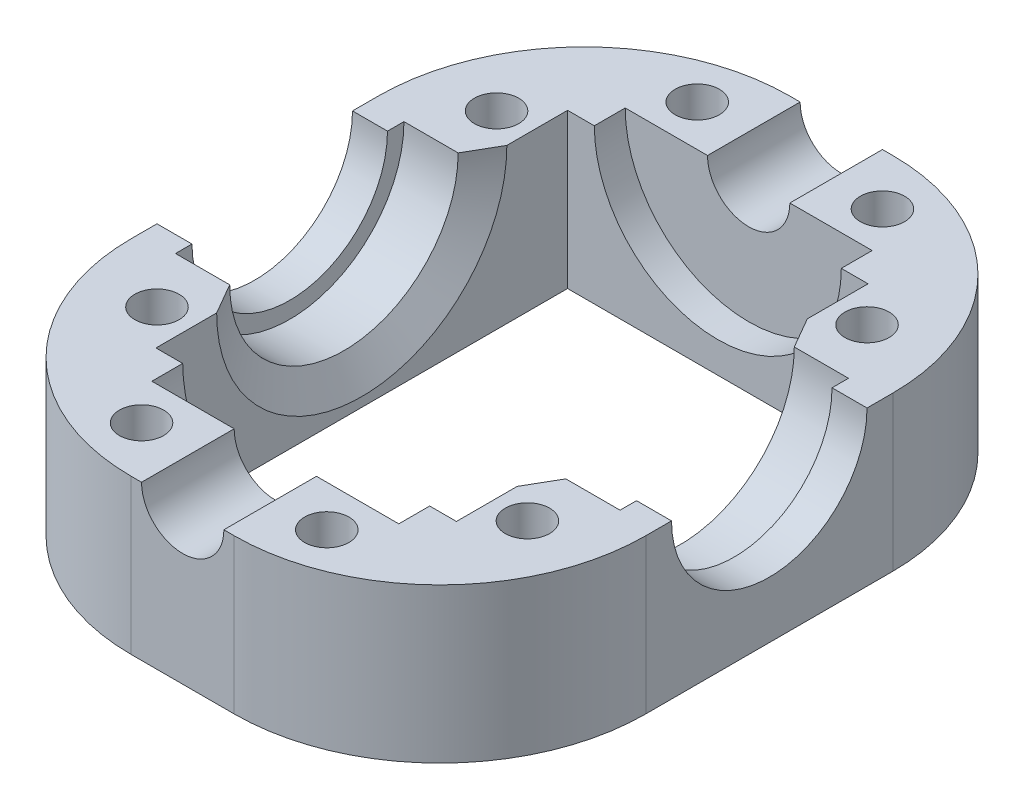
SolidWorks part; units mm, degrees
ref_plane "Спереди" through (0, 0, 0) normal (0, 0, 1) x (1, 0, 0)
ref_plane "Сверху" through (0, 0, 0) normal (0, 1, 0) x (1, 0, 0)
ref_plane "Справа" through (0, 0, 0) normal (1, 0, 0) x (0, 0, -1)
sketch "Sketch1" plane through (0, 0, 0) normal (0, 1, 0) x (1, 0, 0)
  line L1 (25, -32) -> (-25, -32)
  line L2 (25, -32) -> (25, 32)
  line L3 (25, 32) -> (-25, 32)
  line L4 (-25, -32) -> (-25, 32)
  line L5 (25, -32) -> (-25, 32) construction
  line L6 (25, 32) -> (-25, -32) construction
  line L7 (14.6, -20) -> (-14.6, -20)
  line L8 (14.6, -20) -> (14.6, 20)
  line L9 (14.6, 20) -> (-14.6, 20)
  line L10 (-14.6, -20) -> (-14.6, 20)
  line L11 (14.6, -20) -> (-14.6, 20) construction
  line L12 (14.6, 20) -> (-14.6, -20) construction
  point P0 (0, 0)
  point P6 (0, 0)
  dimension "D1" = 50
  dimension "D2" = 64
  dimension "D3" = 40
  dimension "D4" = 29.2
extrude "Boss-Extrude1" add sketch "Sketch1" along normal blind 15
sketch "Sketch3" plane through (0, 15, 0) normal (0, 1, 0) x (1, 0, 0)
  line L0 (-14.6, 0) -> (-25, 0) construction
  line L1 (-14.6, 20) -> (-14.6, -20) construction
  line L2 (-25, 32) -> (-25, -32) construction
  line L3 (14.6, 0) -> (25, 0) construction
  line L4 (14.6, -20) -> (14.6, 20) construction
  line L5 (25, -32) -> (25, 32) construction
  line L10 (14.6, -11.1) -> (21.6, -11.1)
  line L11 (14.6, -11.1) -> (14.6, 0)
  line L12 (14.6, 0) -> (21.6, 0)
  line L13 (21.6, -11.1) -> (21.6, 0)
  line L14 (14.6, -11.1) -> (21.6, 0) construction
  line L15 (14.6, 0) -> (21.6, -11.1) construction
  line L16 (-21.6, -11.1) -> (-14.6, -11.1)
  line L17 (-21.6, -11.1) -> (-21.6, 0)
  line L18 (-21.6, 0) -> (-14.6, 0)
  line L19 (-14.6, -11.1) -> (-14.6, 0)
  line L20 (-21.6, -11.1) -> (-14.6, 0) construction
  line L21 (-21.6, 0) -> (-14.6, -11.1) construction
  point P18 (18.1, -5.55)
  point P23 (-18.1, -5.55)
  dimension "D1" = 7
  dimension "D2" = 11.1
revolve "Cut-Revolve1" cut sketch "Sketch3" angle 360 about L12
sketch "Sketch4" plane through (25, 0, 0) normal (1, 0, 0) x (0, 0, -1)
  line L0 (-32, 15) -> (32, 15) construction
  circle A0 centre (0, 15) radius 9.5
  dimension "D1" = 19
extrude "Cut-Extrude2" cut sketch "Sketch4" against normal through all
sketch "Sketch5" plane through (0, 0, 32) normal (0, 0, 1) x (1, 0, 0)
  line L0 (-25, 15) -> (25, 15) construction
  circle A0 centre (0, 15) radius 4
  dimension "D1" = 8
extrude "Cut-Extrude3" cut sketch "Sketch5" against normal through all
sketch "Sketch8" plane through (0, 15, 0) normal (0, 1, 0) x (1, 0, 0)
  line L1 (-18, -16.5) -> (18, -16.5) construction
  line L2 (-18, -16.5) -> (-18, 16.5) construction
  line L3 (-18, 16.5) -> (18, 16.5) construction
  line L4 (18, -16.5) -> (18, 16.5) construction
  line L5 (-18, -16.5) -> (18, 16.5) construction
  line L6 (-18, 16.5) -> (18, -16.5) construction
  line L7 (-9, 27) -> (9, 27) construction
  line L8 (-9, 27) -> (-9, -27) construction
  line L9 (-9, -27) -> (9, -27) construction
  line L10 (9, 27) -> (9, -27) construction
  line L11 (-9, 27) -> (9, -27) construction
  line L12 (-9, -27) -> (9, 27) construction
  circle A0 centre (18, 16.5) radius 2.15
  circle A1 centre (18, -16.5) radius 2.15
  circle A2 centre (-18, -16.5) radius 2.15
  circle A3 centre (-18, 16.5) radius 2.15
  circle A4 centre (9, -27) radius 2.15
  circle A5 centre (-9, -27) radius 2.15
  circle A6 centre (-9, 27) radius 2.15
  circle A7 centre (9, 27) radius 2.15
  point P0 (0, 0)
  point P10 (0, 0)
  dimension "D3" = 4.3
  dimension "D1" = 33
  dimension "D2" = 36
  dimension "D4" = 18
  dimension "D5" = 54
extrude "Cut-Extrude6" cut sketch "Sketch8" against normal through all
fillet "Fillet1" radius 20 4 edges at (-25, 7.5, 32) (-25, 7.5, -32) (25, 7.5, -32) (25, 7.5, 32)
chamfer "Chamfer1" distance 3 angle 30 2 edges at (-14.6, 3.9, 0) (14.6, 3.9, 0)
sketch "Sketch9" plane through (0, 15, 0) normal (0, 1, 0) x (1, 0, 0)
  line L0 (0, 29.8714) -> (0, -31.0419) construction
  line L1 (-4, 20) -> (-14.6, 20) construction
  line L2 (-12, -23) -> (0, -23)
  line L3 (-12, -23) -> (-12, -20)
  line L4 (-12, -20) -> (0, -20)
  line L5 (0, -23) -> (0, -20)
  line L6 (-12, -23) -> (0, -20) construction
  line L7 (-12, -20) -> (0, -23) construction
  line L8 (-12, 20) -> (0, 20)
  line L9 (-12, 20) -> (-12, 23)
  line L10 (-12, 23) -> (0, 23)
  line L11 (0, 20) -> (0, 23)
  line L12 (-12, 20) -> (0, 23) construction
  line L13 (-12, 23) -> (0, 20) construction
  line L14 (-14.6, -20) -> (-4, -20) construction
  point P3 (-6, -21.5)
  point P8 (-6, 21.5)
  dimension "D1" = 3
  dimension "D2" = 12
revolve "Cut-Revolve2" cut sketch "Sketch9" angle 360 about L0
